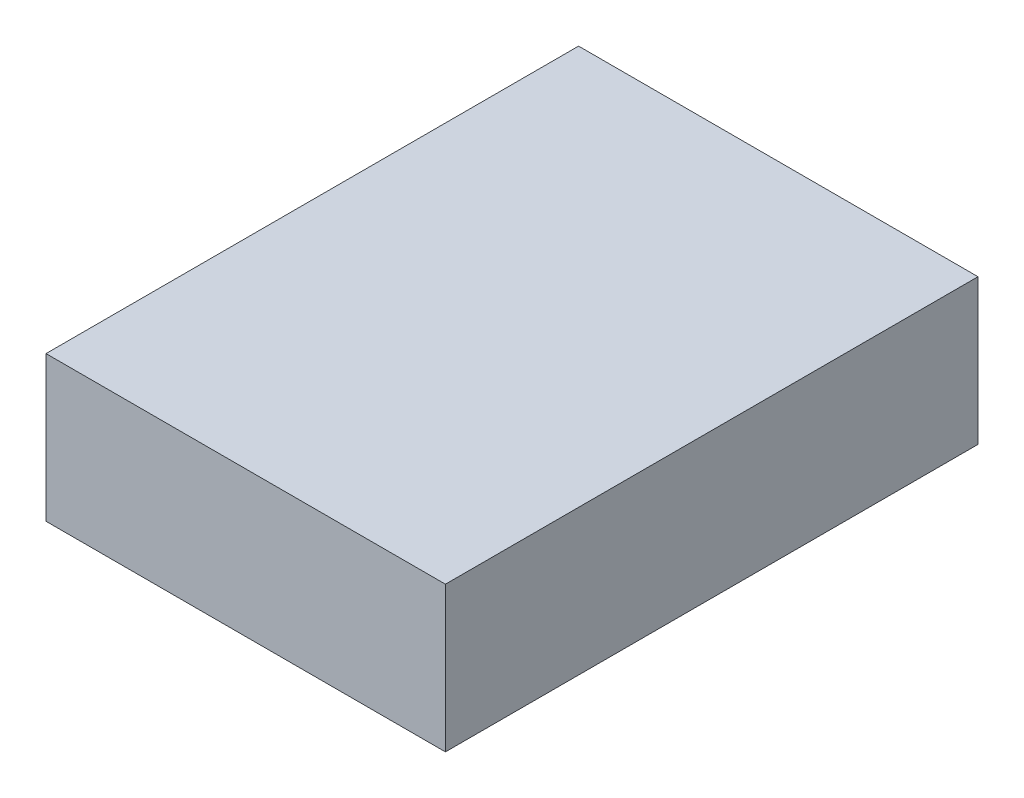
SolidWorks part; units mm, degrees
material "Pine"
ref_plane "Front Plane" through (0, 0, 0) normal (0, 0, 1) x (1, 0, 0)
ref_plane "Top Plane" through (0, 0, 0) normal (0, 1, 0) x (1, 0, 0)
ref_plane "Right Plane" through (0, 0, 0) normal (1, 0, 0) x (0, 0, -1)
sketch "Sketch1" plane through (0, 0, 0) normal (0, 1, 0) x (1, 0, 0)
  line L1 (0, 0) -> (52.3875, 0)
  line L2 (0, 0) -> (0, 69.85)
  line L3 (0, 69.85) -> (52.3875, 69.85)
  line L4 (52.3875, 0) -> (52.3875, 69.85)
  dimension "D1" = 69.85
  dimension "D2" = 52.3875
extrude "Boss-Extrude1" add sketch "Sketch1" along normal blind 19.05
